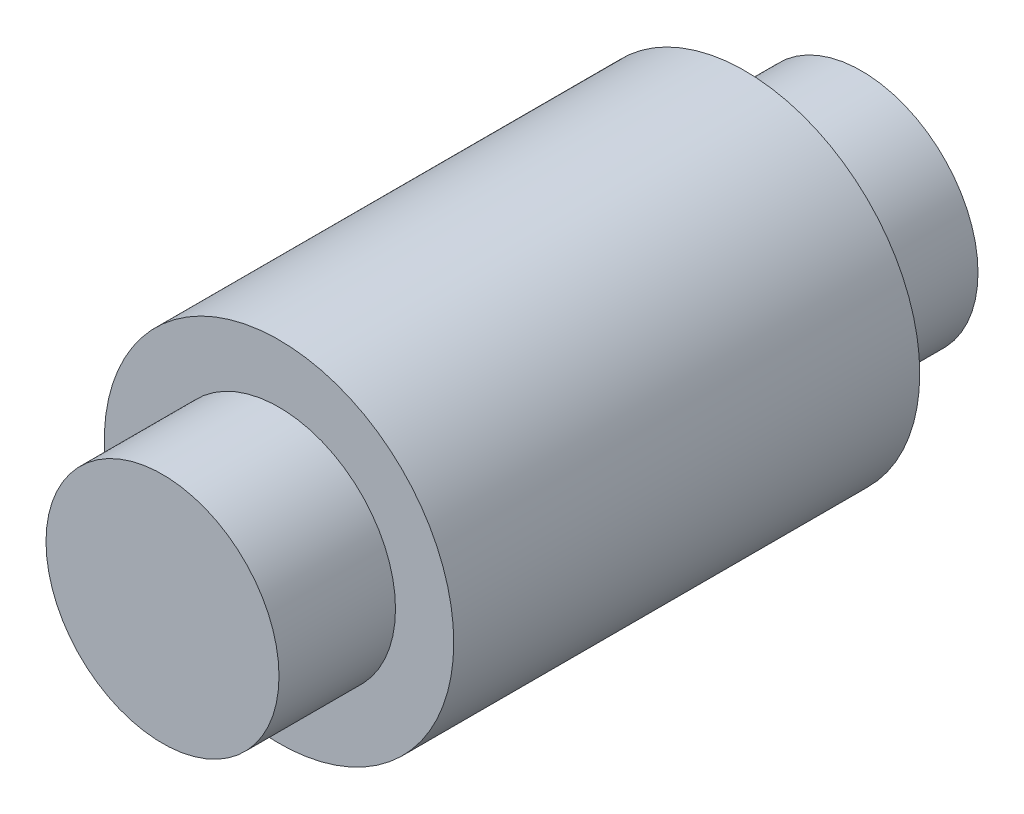
SolidWorks part; units mm, degrees
ref_plane "Front Plane" through (0, 0, 0) normal (0, 0, 1) x (1, 0, 0)
ref_plane "Top Plane" through (0, 0, 0) normal (0, 1, 0) x (1, 0, 0)
ref_plane "Right Plane" through (0, 0, 0) normal (1, 0, 0) x (0, 0, -1)
sketch "Sketch1" plane through (0, 0, 0) normal (0, 0, 1) x (1, 0, 0)
  circle A0 centre (0, 0) radius 7.5
  dimension "D1" = 15
extrude "Boss-Extrude1" add sketch "Sketch1" along normal mid plane 20
sketch "Sketch2" plane through (0, 0, 0) normal (0, 0, 1) x (1, 0, 0)
  circle A0 centre (0, 0) radius 5
  dimension "D1" = 10
extrude "Boss-Extrude2" add sketch "Sketch2" along normal mid plane 30
